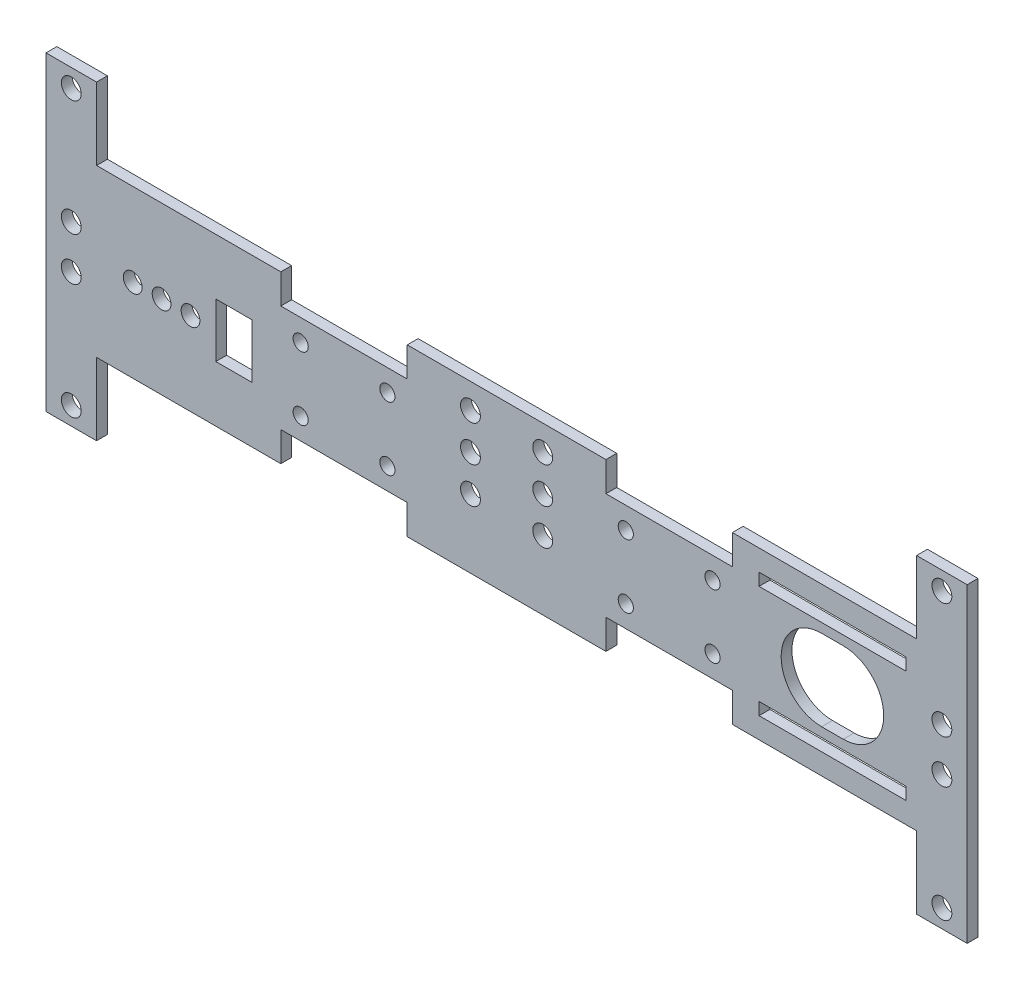
SolidWorks part; units mm, degrees
ref_plane "Plan de face" through (0, 0, 0) normal (0, 0, 1) x (1, 0, 0)
ref_plane "Plan de dessus" through (0, 0, 0) normal (0, 1, 0) x (1, 0, 0)
ref_plane "Plan de droite" through (0, 0, 0) normal (1, 0, 0) x (0, 0, -1)
ref_plane "Plan1" through (0, 0, 0) normal (0, 0, -1) x (-1, 0, 0)
sketch "Esquisse1" plane through (0, 0, 0) normal (0, 0, -1) x (-1, 0, 0)
  line L0 (-238, 60.2) -> (-197.4, 60.2)
  line L1 (-197.4, 60.2) -> (-197.4, 56.8)
  line L2 (-197.4, 56.8) -> (-238, 56.8)
  line L3 (-238, 56.8) -> (-238, 60.2)
  line L4 (-214.7, 31.8) -> (-220.7, 31.8)
  line L5 (-220.7, 54.2) -> (-214.7, 54.2)
  line L6 (-197.4, 29.2) -> (-197.4, 25.8)
  line L7 (-197.4, 25.8) -> (-238, 25.8)
  line L8 (-238, 25.8) -> (-238, 29.2)
  line L9 (-238, 29.2) -> (-197.4, 29.2)
  line L11 (-47, 50.5) -> (-57, 50.5)
  line L12 (-47, 50.5) -> (-47, 35.5)
  line L13 (-47, 35.5) -> (-57, 35.5)
  line L14 (-14, 66) -> (-241, 66)
  line L15 (-241, 66) -> (-241, 86)
  line L16 (-241, 86) -> (-255, 86)
  line L17 (-255, 86) -> (-255, 20)
  line L18 (-255, 0) -> (-241, 0)
  line L19 (-241, 0) -> (-241, 20)
  line L20 (-241, 20) -> (-14, 20)
  line L21 (-14, 20) -> (-14, 0)
  line L22 (-14, 0) -> (0, 0)
  line L23 (0, 0) -> (0, 86)
  line L24 (0, 86) -> (-14, 86)
  line L25 (-14, 86) -> (-14, 66)
  line L26 (-214.7, 43) -> (-220.7, 43) construction
  line L27 (-248, 81) -> (-248, 5) construction
  line L28 (-238, 56.8) -> (-238, 29.2) construction
  line L32 (-255, 20) -> (-255, 0)
  line L33 (-7, 81) -> (-7, 5) construction
  line L34 (-70.5, 51.805) -> (-94.5, 51.805) construction
  line L35 (-70.5, 51.805) -> (-70.5, 34.195) construction
  line L36 (-70.5, 34.195) -> (-94.5, 34.195) construction
  line L37 (-94.5, 51.805) -> (-94.5, 34.195) construction
  line L38 (-160.5, 51.805) -> (-184.5, 51.805) construction
  line L39 (-160.5, 51.805) -> (-160.5, 34.195) construction
  line L40 (-160.5, 34.195) -> (-184.5, 34.195) construction
  line L41 (-184.5, 51.805) -> (-184.5, 34.195) construction
  line L42 (-117.5, 59) -> (-137.5, 59) construction
  line L43 (-117.5, 59) -> (-117.5, 39) construction
  line L44 (-117.5, 39) -> (-137.5, 39) construction
  line L45 (-137.5, 59) -> (-137.5, 39) construction
  line L46 (-24, 43) -> (-40, 43) construction
  line L47 (-57, 50.5) -> (-57, 35.5)
  line L48 (-47, 50.5) -> (-57, 35.5) construction
  line L49 (-47, 35.5) -> (-57, 50.5) construction
  circle A0 centre (-7, 81) radius 2.75
  circle A1 centre (-32, 43) radius 2.6
  circle A2 centre (-40, 43) radius 2.6
  circle A3 centre (-137.5, 39) radius 2.75
  circle A4 centre (-117.5, 39) radius 2.75
  circle A5 centre (-137.5, 59) radius 2.75
  circle A6 centre (-117.5, 59) radius 2.75
  circle A7 centre (-94.5, 51.805) radius 2.1
  circle A8 centre (-248, 37) radius 2.75
  circle A9 centre (-248, 5) radius 2.75
  circle A10 centre (-248, 49) radius 2.75
  circle A11 centre (-117.5, 49) radius 2.75
  circle A12 centre (-137.5, 49) radius 2.75
  circle A13 centre (-160.5, 51.805) radius 2.1
  circle A14 centre (-94.5, 34.195) radius 2.1
  circle A15 centre (-70.5, 34.195) radius 2.1
  arc A16 (-220.7, 31.8) -> (-220.7, 54.2) centre (-220.7, 43) cw
  arc A17 (-214.7, 54.2) -> (-214.7, 31.8) centre (-214.7, 43) cw
  circle A18 centre (-70.5, 51.805) radius 2.1
  circle A19 centre (-184.5, 34.195) radius 2.1
  circle A20 centre (-7, 37) radius 2.75
  circle A21 centre (-248, 81) radius 2.75
  circle A22 centre (-24, 43) radius 2.6
  circle A23 centre (-184.5, 51.805) radius 2.1
  circle A24 centre (-7, 5) radius 2.75
  circle A25 centre (-7, 49) radius 2.75
  circle A26 centre (-160.5, 34.195) radius 2.1
  point P34 (-127.5, 59)
  point P62 (-7, 86)
  point P64 (-52, 43)
  point P80 (0, 43)
  point P82 (-217.7, 43)
  point P83 (-248, 43)
  point P84 (-217.7, 56.8)
  point P85 (-238, 43)
  point P86 (-70.5, 43)
  point P87 (-127.5, 66)
  point P88 (-248, 86)
  point P94 (-117.5, 49)
  point P96 (-137.5, 49)
  point P98 (-127.5, 39)
  point P101 (-32, 43)
  dimension "D8" = 11.2
  dimension "D13" = 5.5
  dimension "D22" = 5.5
  dimension "D25" = 4.2
  dimension "D30" = 5.2
  dimension "D2" = 86
  dimension "D3" = 20
  dimension "D4" = 14
  dimension "D5" = 3.4
  dimension "D6" = 40.6
  dimension "D7" = 27.6
  dimension "D9" = 6
  dimension "D10" = 32
  dimension "D11" = 32
  dimension "D12" = 76
  dimension "D14" = 255
  dimension "D15" = 3
  dimension "D17" = 24
  dimension "D18" = 17.61
  dimension "D19" = 66
  dimension "D21" = 20
  dimension "D23" = 7
  dimension "D24" = 33
  dimension "D26" = 10
  dimension "D27" = 15
  dimension "D28" = 16
  dimension "D29" = 24
  dimension "D31" = 7
extrude "Boss.-Extru.1" add sketch "Esquisse1" against normal blind 3
sketch "Esquisse2" plane through (0, 0, 3) normal (0, 0, 1) x (1, 0, 0)
  line L0 (14, 66) -> (241, 66) construction
  line L1 (65, 66) -> (100, 66)
  line L2 (65, 66) -> (65, 57.805)
  line L3 (65, 57.805) -> (100, 57.805)
  line L4 (100, 66) -> (100, 57.805)
  line L6 (70.5, 51.805) -> (94.5, 51.805) construction
  line L8 (0, 43) -> (255, 43) construction
  line L9 (0, 0) -> (0, 86) construction
  line L10 (255, 86) -> (255, 20) construction
  line L11 (127.5, 66) -> (127.5, 20) construction
  line L12 (14, 66) -> (241, 66) construction
  line L13 (241, 20) -> (14, 20) construction
  line L14 (65, 28.195) -> (100, 28.195)
  line L15 (100, 20) -> (100, 28.195)
  line L16 (65, 20) -> (100, 20)
  line L17 (65, 20) -> (65, 28.195)
  line L18 (190, 20) -> (190, 28.195)
  line L19 (190, 20) -> (155, 20)
  line L20 (155, 20) -> (155, 28.195)
  line L21 (190, 28.195) -> (155, 28.195)
  line L22 (190, 57.805) -> (155, 57.805)
  line L23 (155, 66) -> (155, 57.805)
  line L24 (190, 66) -> (155, 66)
  line L25 (190, 66) -> (190, 57.805)
  point P6 (82.5, 51.805)
  point P9 (82.5, 57.805)
  dimension "D1" = 35
  dimension "D2" = 6
extrude "Enlèv. mat.-Extru.1" cut sketch "Esquisse2" against normal up to next
